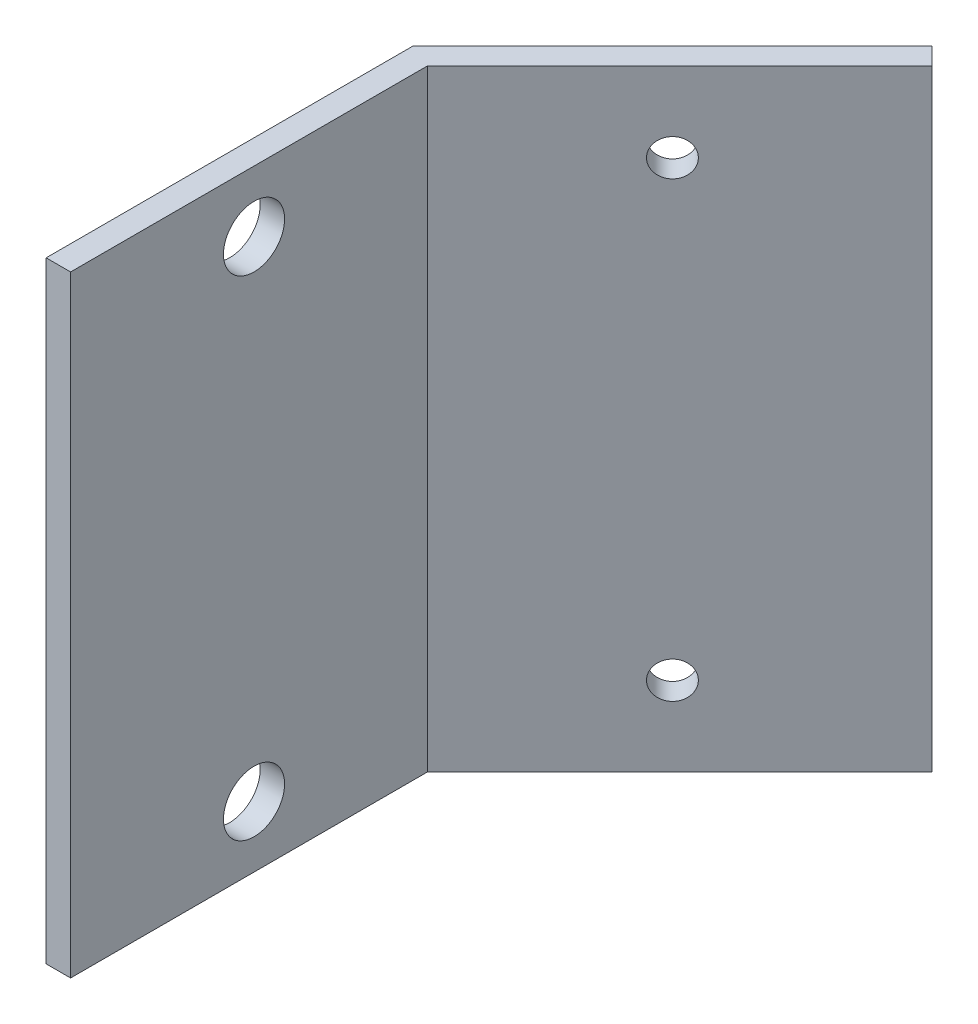
SolidWorks part; units mm, degrees
ref_plane "Plan de face" through (0, 0, 0) normal (0, 0, 1) x (1, 0, 0)
ref_plane "Plan de dessus" through (0, 0, 0) normal (0, 1, 0) x (1, 0, 0)
ref_plane "Plan de droite" through (0, 0, 0) normal (1, 0, 0) x (0, 0, -1)
sketch "Esquisse1" plane through (0, 0, 0) normal (0, 1, 0) x (1, 0, 0)
  line L0 (0, 0) -> (0, 30)
  line L1 (0, 30) -> (21.2132, 51.2132)
  line L2 (21.2132, 51.2132) -> (22.6274, 49.799)
  line L3 (22.6274, 49.799) -> (2, 29.1716)
  line L4 (2, 29.1716) -> (2, 0)
  line L5 (2, 0) -> (0, 0)
  dimension "D1" = 2
  dimension "D2" = 30
  dimension "D3" = 45
extrude "Extrusion1" add sketch "Esquisse1" along normal blind 50
sketch "Esquisse3" plane through (0, 0, 0) normal (-1, 0, 0) x (0, 0, 1)
  line L0 (-15, 0) -> (-15, 50) construction
  line L1 (-30, 0) -> (0, 0) construction
  line L2 (-30, 50) -> (0, 50) construction
  line L3 (0, 25) -> (-30, 25) construction
  line L4 (0, 50) -> (0, 0) construction
  line L5 (-30, 50) -> (-30, 0) construction
  line L6 (0, 5) -> (-30, 5) construction
  circle A0 centre (-15, 5) radius 2.5
  circle A1 centre (-15, 45) radius 2.5
  dimension "D1" = 5
  dimension "D2" = 5
extrude "Extrusion2" cut sketch "Esquisse3" against normal up to next
sketch "Esquisse4" plane through (-15, 0, -15) normal (-0.7071, 0, -0.7071) x (-0.7071, 0, 0.7071)
  line L0 (-36.2132, 50) -> (-36.2132, 0) construction
  line L1 (-51.2132, 50) -> (-21.2132, 50) construction
  line L2 (-51.2132, 0) -> (-21.2132, 0) construction
  line L3 (-51.2132, 25) -> (-21.2132, 25) construction
  line L4 (-51.2132, 50) -> (-51.2132, 0) construction
  line L5 (-21.2132, 50) -> (-21.2132, 0) construction
  line L6 (-51.2132, 43.5) -> (-21.2132, 43.5) construction
  circle A0 centre (-36.2132, 43.5) radius 1.5
  circle A1 centre (-36.2132, 6.5) radius 1.5
  dimension "D2" = 3
  dimension "D1" = 18.5
extrude "Extrusion3" cut sketch "Esquisse4" against normal up to next
